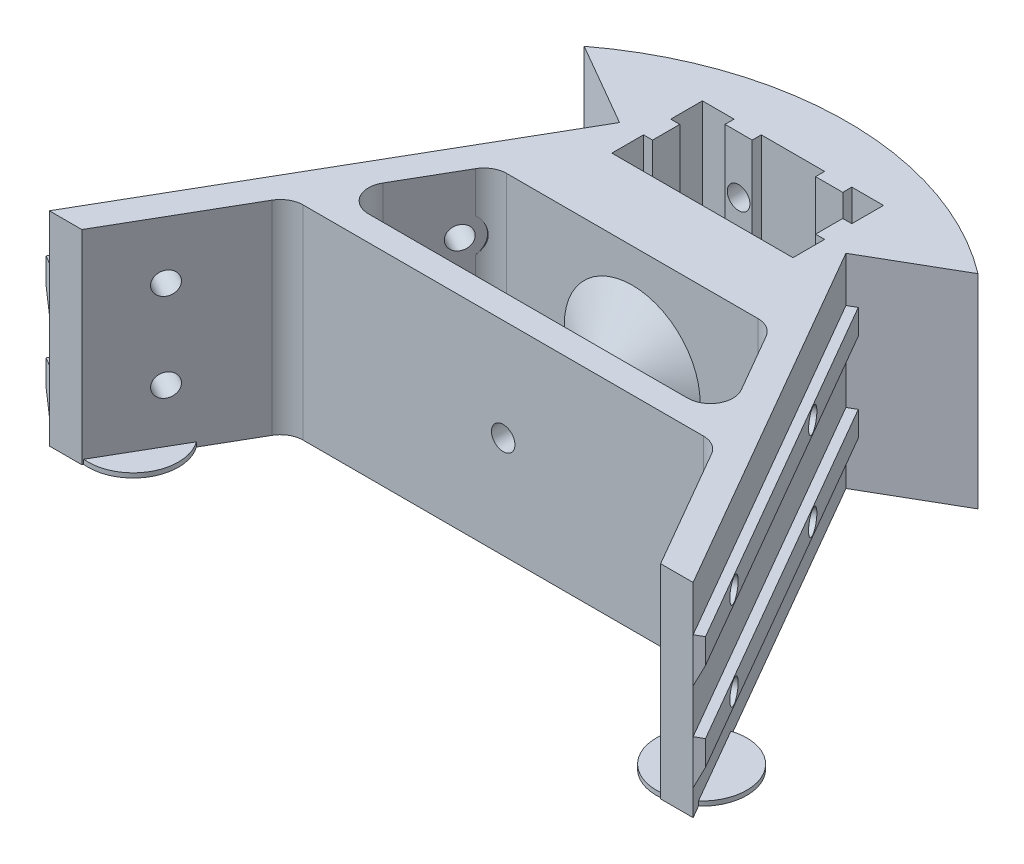
SolidWorks part; units mm, degrees
material "ABS"
ref_plane "Front Plane" through (0, 0, 0) normal (0, 0, 1) x (1, 0, 0)
ref_plane "Top Plane" through (0, 0, 0) normal (0, 1, 0) x (1, 0, 0)
ref_plane "Right Plane" through (0, 0, 0) normal (1, 0, 0) x (0, 0, -1)
sketch "Sketch1" plane through (0, 0, 0) normal (0, 1, 0) x (1, 0, 0)
  line L0 (0, -40) -> (0, 0) construction
  line L1 (-20, 20) -> (-13, 20)
  line L2 (-13, 20) -> (-13, 18)
  line L3 (-13, 18) -> (-7, 18)
  line L4 (-7, 18) -> (-7, 20)
  line L5 (-7, 20) -> (7, 20)
  line L6 (7, 20) -> (7, 18)
  line L7 (7, 18) -> (13, 18)
  line L8 (13, 18) -> (13, 20)
  line L9 (13, 20) -> (20, 20)
  line L10 (20, 20) -> (20, 13)
  line L11 (20, 13) -> (18, 13)
  line L12 (18, 13) -> (18, 7)
  line L13 (18, 7) -> (20, 7)
  line L14 (20, 7) -> (20, 0)
  line L15 (0, 20) -> (0, 0) construction
  line L16 (0, 0) -> (0, 50) construction
  line L17 (0, 50) -> (7.5492, 36.9243) construction
  line L18 (34.641, 70) -> (134.641, -103.2051) construction
  line L19 (20, 0) -> (-20, 0)
  line L20 (0, 50) -> (34.641, 70) construction
  line L21 (134.641, -103.2051) -> (100, -123.2051) construction
  line L22 (67.0736, -66.1749) -> (25, 6.6987)
  line L23 (25, 6.6987) -> (43.4956, 17.3771)
  line L24 (-20, 0) -> (-20, 7)
  line L25 (-20, 7) -> (-18, 7)
  line L26 (-18, 7) -> (-18, 13)
  line L27 (-18, 13) -> (-20, 13)
  line L28 (-20, 13) -> (-20, 20)
  line L29 (59.641, 26.6987) -> (134.641, -103.2051) construction
  line L30 (0, 50) -> (-7.0324, 37.8196) construction
  line L31 (0, 50) -> (-34.641, 70) construction
  line L32 (-34.641, 70) -> (-134.641, -103.2051) construction
  line L33 (-134.641, -103.2051) -> (-59.641, 26.6987) construction
  line L34 (-43.4956, 17.3771) -> (-25, 6.6987)
  line L35 (-25, 6.6987) -> (-67.0736, -66.1749)
  line L36 (-100, -123.2051) -> (-134.641, -103.2051) construction
  line L37 (0, -40) -> (0, -15.5) construction
  line L38 (-27.7444, -15.5) -> (27.7444, -15.5)
  line L39 (-35.25, -38.5) -> (35.25, -38.5)
  line L40 (-32.0746, -18) -> (-39.5801, -31)
  line L41 (32.0746, -18) -> (39.5801, -31)
  line L42 (-39.5801, -31) -> (-44.9691, -27.8887) construction
  line L43 (-39.5801, -31) -> (-47.1202, -44.0598) construction
  line L44 (-32.0746, -18) -> (-43.2264, -37.3156) construction
  line L45 (-37.4635, -14.8887) -> (-32.0746, -18) construction
  line L46 (-48.5291, -46.5) -> (-63.915, -73.1492)
  line L47 (-44.1989, -44) -> (44.1989, -44)
  line L48 (32.0746, -18) -> (39.5801, -31) construction
  line L49 (39.5801, -31) -> (48.7394, -46.8643) construction
  line L50 (48.5291, -46.5) -> (63.915, -73.1492)
  line L51 (-67.0736, -66.1749) -> (-71.1002, -73.1492)
  line L52 (-71.1002, -73.1492) -> (-63.915, -73.1492)
  line L53 (67.0736, -66.1749) -> (71.1002, -73.1492)
  line L54 (71.1002, -73.1492) -> (63.915, -73.1492)
  arc A0 (63.915, -73.1492) -> (67.0736, -66.1749) centre (0, -40) ccw construction
  arc A1 (-27.7444, -15.5) -> (-32.0746, -18) centre (-27.7444, -20.5) ccw
  arc A2 (32.0746, -18) -> (27.7444, -15.5) centre (27.7444, -20.5) ccw
  arc A3 (35.25, -38.5) -> (39.5801, -31) centre (35.25, -33.5) ccw
  arc A4 (-39.5801, -31) -> (-35.25, -38.5) centre (-35.25, -33.5) ccw
  arc A5 (-44.1989, -44) -> (-48.5291, -46.5) centre (-44.1989, -49) ccw
  arc A6 (48.5291, -46.5) -> (44.1989, -44) centre (44.1989, -49) ccw
  arc A7 (-67.0736, -66.1749) -> (-63.915, -73.1492) centre (0, -40) ccw construction
  arc A8 (43.4956, 17.3771) -> (-43.4956, 17.3771) centre (0, -40) ccw
  dimension "D1" = 144
  dimension "D14" = 10
  dimension "D2" = 40
  dimension "D3" = 6
  dimension "D4" = 2
  dimension "D5" = 40
  dimension "D6" = 20
  dimension "D7" = 50
  dimension "D8" = 30
  dimension "D9" = 40
  dimension "D10" = 200
  dimension "D11" = 150
  dimension "D12" = 30
  dimension "D13" = 1.5
  dimension "D15" = 13
  dimension "D17" = 70.5
  dimension "D18" = 5.5
extrude "Boss-Extrude1" add sketch "Sketch1" along normal blind 45
sketch "Sketch3" plane through (21.6506, 0, -12.5) normal (0.866, 0, -0.5) x (-0.5, 0, -0.866)
  line L0 (-98.8992, 35) -> (-6.6987, 35)
  line L1 (-98.8992, 45) -> (-98.8992, 0) construction
  line L2 (-6.6987, 45) -> (-6.6987, 0) construction
  line L3 (-6.6987, 35) -> (-6.6987, 29.5)
  line L4 (-6.6987, 29.5) -> (-98.8992, 29.5)
  line L5 (-98.8992, 29.5) -> (-98.8992, 35)
  line L6 (-98.8992, 15.5) -> (-6.6987, 15.5)
  line L7 (-6.6987, 15.5) -> (-6.6987, 10)
  line L8 (-6.6987, 10) -> (-98.8992, 10)
  line L9 (-98.8992, 10) -> (-98.8992, 15.5)
  line L10 (-98.8992, 22.5) -> (-6.6987, 22.5) construction
  line L11 (-6.6987, 45) -> (-6.6987, 0) construction
  line L12 (-98.8992, 22.5) -> (-98.8992, 29.5) construction
  line L13 (-98.8992, 22.5) -> (-98.8992, 15.5) construction
  dimension "D1" = 5.5
  dimension "D2" = 7
extrude "Boss-Extrude2" add sketch "Sketch3" along normal blind 2
sketch "Sketch4" plane through (23.3827, 0, -13.5) normal (0.866, 0, -0.5) x (-0.5, 0, -0.866)
  line L0 (-6.6987, 32.25) -> (-98.8992, 32.25) construction
  line L1 (-6.6987, 29.5) -> (-6.6987, 35) construction
  line L2 (-98.8992, 35) -> (-98.8992, 29.5) construction
  line L3 (-98.8992, 12.75) -> (-6.6987, 12.75) construction
  line L4 (-98.8992, 15.5) -> (-98.8992, 10) construction
  line L5 (-6.6987, 10) -> (-6.6987, 15.5) construction
  line L6 (-6.6987, 45) -> (-6.6987, 0) construction
  circle A0 centre (-34.1987, 32.25) radius 2.5
  circle A1 centre (-34.1987, 12.75) radius 2.5
  circle A2 centre (-81.6987, 12.75) radius 2.5
  circle A3 centre (-81.6987, 32.25) radius 2.5
  dimension "D1" = 5
  dimension "D3" = 75
  dimension "D2" = 27.5
extrude "Cut-Extrude2" cut sketch "Sketch4" against normal up to next (8.2226 mm away)
sketch "Sketch8" plane through (16.2617, 0, -9.3887) normal (-0.866, 0, 0.5) x (0.5, 0, 0.866)
  circle A0 centre (34.1987, 32.25) radius 4.5
  circle A1 centre (34.1987, 12.75) radius 4.5
  dimension "D1" = 9
extrude "Cut-Extrude7" cut sketch "Sketch8" along normal up to next
sketch "Sketch5" plane through (0, 0, -18) normal (0, 0, 1) x (1, 0, 0)
  line L0 (7, 22.5) -> (13, 22.5) construction
  line L1 (7, 45) -> (7, 0) construction
  line L2 (13, 45) -> (13, 0) construction
  line L3 (10, 22.5) -> (10, 32.5) construction
  line L4 (10, 22.5) -> (10, 12.5) construction
  circle A0 centre (10, 32.5) radius 2.5
  circle A1 centre (10, 12.5) radius 2.5
  dimension "D1" = 20
  dimension "D2" = 5
extrude "Cut-Extrude3" cut sketch "Sketch5" against normal up to next
sketch "Sketch6" plane through (0, 0, -18) normal (0, 0, 1) x (1, 0, 0)
  circle A0 centre (10, 32.5) radius 4.25
  circle A1 centre (10, 12.5) radius 4.25
  dimension "D1" = 8.5
extrude "Cut-Extrude5" cut sketch "Sketch6" along normal blind 1.7 from offset 14 offset against normal yes
mirror "Mirror1" about plane through (0, 0, 0) normal (1, 0, 0) of "Cut-Extrude7", "Cut-Extrude5", "Cut-Extrude3", "Cut-Extrude2", "Boss-Extrude2"
sketch "Sketch7" plane through (0, 45, 0) normal (0, 1, 0) x (1, 0, 0)
  line L0 (-2.6, -5.6) -> (-2.6, -8.4)
  line L1 (2.6, -5.6) -> (2.6, -8.4)
  line L4 (-20, 0) -> (20, 0) construction
  line L5 (0, 0) -> (0, -5.6) construction
  arc A0 (2.6, -5.6) -> (-2.6, -5.6) centre (0, -5.6) ccw
  arc A1 (-2.6, -8.4) -> (2.6, -8.4) centre (0, -8.4) ccw
  dimension "D1" = 5.2
  dimension "D2" = 2.8
  dimension "D3" = 5.6
extrude "Cut-Extrude6" [suppressed] cut sketch "Sketch7" against normal up to next
sketch "Sketch9" plane through (0, 0, 0) normal (1, 0, 0) x (0, 0, -1)
  line L0 (-15.5, 22.5) -> (-38.5, 22.5) construction
  line L1 (-15.5, 45) -> (-15.5, 0) construction
  line L2 (-31.1, 26.1) -> (-31.1, 22.5)
  line L3 (-22.9, 26.1) -> (-15.5, 37.5)
  line L4 (0, 45) -> (0, 0) construction
  line L5 (-38.5, 37.5) -> (-31.1, 26.1)
  line L6 (-38.5, 45) -> (-38.5, 0) construction
  line L7 (-31.1, 22.5) -> (-38.5, 22.5)
  line L8 (-38.5, 22.5) -> (-38.5, 37.5)
  line L9 (-22.9, 26.1) -> (-22.9, 22.5)
  line L10 (-22.9, 22.5) -> (-15.5, 22.5)
  line L11 (-15.5, 22.5) -> (-15.5, 37.5)
  dimension "D1" = 8.2
  dimension "D2" = 15
  dimension "D3" = 3.6
  dimension "D4" = 22.9
revolve "Revolve1" add sketch "Sketch9" angle 360 about L0
sketch "Sketch10" plane through (0, 0, 44) normal (0, 0, 1) x (1, 0, 0)
  line L0 (0, 45) -> (0, 0) construction
  line L1 (-44.1989, 45) -> (44.1989, 45) construction
  circle A0 centre (0, 22.5) radius 2.6
  dimension "D1" = 5.2
extrude "Cut-Extrude8" cut sketch "Sketch10" against normal blind 32
sketch "Sketch11" plane through (0, 0, 0) normal (0, 1, 0) x (1, 0, 0)
  line L0 (59.2113, -65.0022) -> (66.3323, -60.8909) construction
  line L1 (48.5291, -46.5) -> (63.915, -73.1492) construction
  line L2 (26.7321, 7.6987) -> (72.8323, -72.1492) construction
  line L3 (-59.2113, -65.0022) -> (-66.3323, -60.8909) construction
  line L4 (-63.915, -73.1492) -> (-48.5291, -46.5) construction
  line L5 (-26.7321, 7.6987) -> (-72.8323, -72.1492) construction
  line L6 (72.8323, -72.1492) -> (71.1002, -73.1492) construction
  circle A0 centre (62.7718, -62.9466) radius 10
  circle A1 centre (-62.7718, -62.9466) radius 10
  dimension "D2" = 20
  dimension "D1" = 13
extrude "Boss-Extrude3" add sketch "Sketch11" along normal blind 1
sketch "Sketch12" plane through (49.4496, 0, 85.6492) normal (0.5, 0, 0.866) x (0.866, 0, -0.5)
  line L0 (25, 29.5) -> (27, 29.5)
  line L1 (27, 29.5) -> (25, 25.211)
  line L2 (25, 29.5) -> (25, 15.5) construction
  line L3 (25, 25.211) -> (25, 29.5)
  line L4 (25, 10) -> (27, 10)
  line L5 (27, 10) -> (25, 5.711)
  line L6 (25, 10) -> (25, 0) construction
  line L7 (25, 5.711) -> (25, 10)
  dimension "D1" = 65
extrude "Boss-Extrude4" add sketch "Sketch12" against normal blind 0.7
pattern_linear "LPattern1" count 46 spacing 2 along (-0.5, 0, -0.866) of "Boss-Extrude4"
sketch "Sketch13" plane through (-49.4496, 0, 85.6492) normal (-0.5, 0, 0.866) x (0.866, 0, 0.5)
  line L0 (-25, 29.5) -> (-27, 29.5)
  line L1 (-27, 29.5) -> (-25, 25.211)
  line L2 (-25, 29.5) -> (-25, 15.5) construction
  line L3 (-25, 25.211) -> (-25, 29.5)
  line L4 (-25, 10) -> (-27, 10)
  line L5 (-27, 10) -> (-25, 5.711)
  line L6 (-25, 10) -> (-25, 0) construction
  line L7 (-25, 5.711) -> (-25, 10)
  dimension "D1" = 65
extrude "Boss-Extrude5" add sketch "Sketch13" against normal blind 0.7
pattern_linear "LPattern2" count 46 spacing 2 along (0.5, 0, -0.866) of "Boss-Extrude5"
equation "\"D12@Sketch1\"=\"D8@Sketch1\""
equation "\"D2@Sketch3\"=(20-6)/2"
equation "\"D4@Sketch9\"=27-\"D1@Sketch9\"/2"
